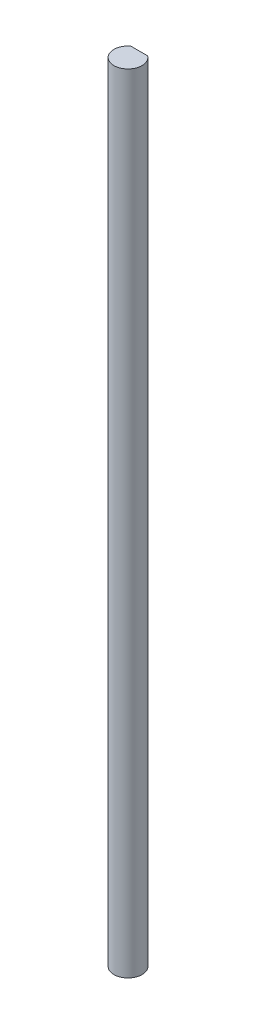
SolidWorks part; units mm, degrees
ref_plane "Front Plane" through (0, 0, 0) normal (0, 0, 1) x (1, 0, 0)
ref_plane "Top Plane" through (0, 0, 0) normal (0, 1, 0) x (1, 0, 0)
ref_plane "Right Plane" through (0, 0, 0) normal (1, 0, 0) x (0, 0, -1)
sketch "Sketch1" plane through (0, 0, 0) normal (0, 1, 0) x (1, 0, 0)
  line L0 (-1.905, 2.54) -> (1.905, 2.54)
  arc A0 (-1.905, 2.54) -> (1.905, 2.54) centre (0, 0) ccw
  dimension "D1" = 6.35
  dimension "D2" = 2.54
extrude "Boss-Extrude1" add sketch "Sketch1" along normal blind 177.8
